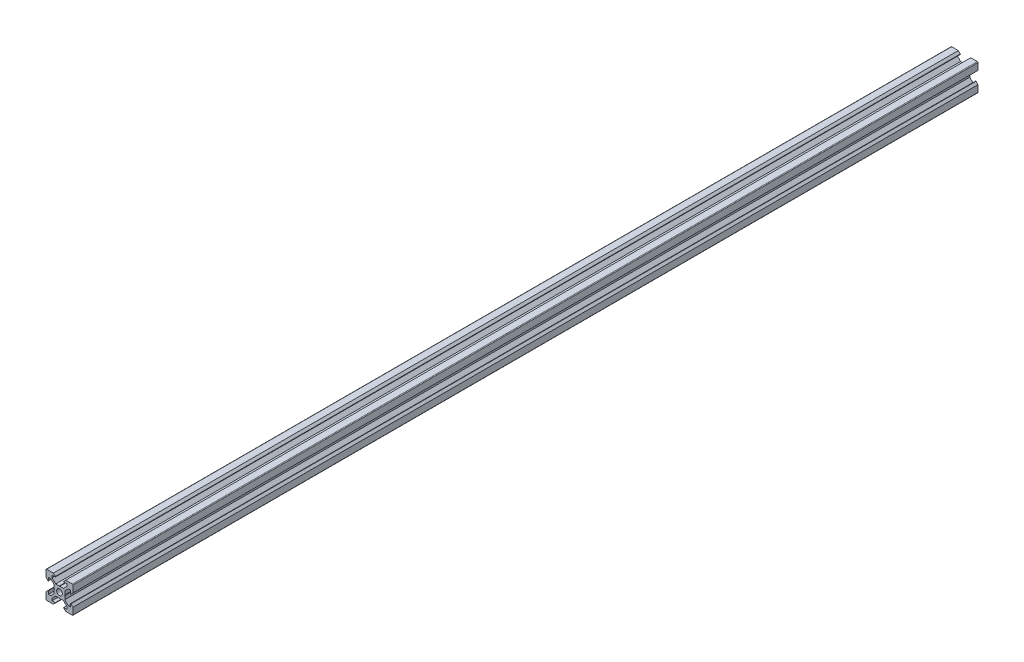
SolidWorks part; units mm, degrees
material "6061-T6 (SS)"
ref_plane "Front Plane" through (0, 0, 0) normal (0, 0, 1) x (1, 0, 0)
ref_plane "Top Plane" through (0, 0, 0) normal (0, 1, 0) x (1, 0, 0)
ref_plane "Right Plane" through (0, 0, 0) normal (1, 0, 0) x (0, 0, -1)
sketch "Sketch1" plane through (0, 0, 0) normal (0, 0, 1) x (1, 0, 0)
  line L1 (9.5, -10) -> (-9.5, -10)
  line L2 (10, -9.5) -> (10, 9.5)
  line L3 (9.5, 10) -> (-9.5, 10)
  line L4 (-10, -9.5) -> (-10, 9.5)
  line L5 (10, -10) -> (-10, 10) construction
  line L6 (10, 10) -> (-10, -10) construction
  circle A0 centre (0, 0) radius 2.1
  arc A1 (-9.5, 10) -> (-10, 9.5) centre (-9.5, 9.5) ccw
  arc A2 (10, 9.5) -> (9.5, 10) centre (9.5, 9.5) ccw
  arc A3 (9.5, -10) -> (10, -9.5) centre (9.5, -9.5) ccw
  arc A4 (-9.5, -10) -> (-10, -9.5) centre (-9.5, -9.5) cw
  point P0 (0, 0)
  line B0 (0, 0) -> (0, 10) construction
  line B1 (0, 3.69) -> (-0.21, 3.9)
  line B2 (-0.21, 3.9) -> (-2.8393, 3.9)
  line B3 (-2.8393, 3.9) -> (-5.5, 6.5607)
  line B4 (-5.5, 6.5607) -> (-5.5, 8.2)
  line B5 (-5.5, 8.2) -> (-3.125, 8.2)
  line B6 (-3.125, 8.2) -> (-3.125, 8.545)
  line B7 (-3.125, 8.545) -> (-4.58, 10)
  line B8 (-4.58, 10) -> (4.58, 10)
  line B9 (0, 0) -> (-5.9132, 5.9132) construction
  line B10 (3.125, 8.545) -> (4.58, 10)
  line B11 (3.125, 8.2) -> (3.125, 8.545)
  line B12 (5.5, 8.2) -> (3.125, 8.2)
  line B13 (5.5, 6.5607) -> (5.5, 8.2)
  line B14 (2.8393, 3.9) -> (5.5, 6.5607)
  line B15 (0.21, 3.9) -> (2.8393, 3.9)
  line B16 (0, 3.69) -> (0.21, 3.9)
  line B17 (0, 0) -> (-10, 0) construction
  line B18 (-3.69, 0) -> (-3.9, -0.21)
  line B19 (-3.9, -0.21) -> (-3.9, -2.8393)
  line B20 (-3.9, -2.8393) -> (-6.5607, -5.5)
  line B21 (-6.5607, -5.5) -> (-8.2, -5.5)
  line B22 (-8.2, -5.5) -> (-8.2, -3.125)
  line B23 (-8.2, -3.125) -> (-8.545, -3.125)
  line B24 (-8.545, -3.125) -> (-10, -4.58)
  line B25 (-10, -4.58) -> (-10, 4.58)
  line B26 (0, 0) -> (-5.9132, -5.9132) construction
  line B27 (-8.545, 3.125) -> (-10, 4.58)
  line B28 (-8.2, 3.125) -> (-8.545, 3.125)
  line B29 (-8.2, 5.5) -> (-8.2, 3.125)
  line B30 (-6.5607, 5.5) -> (-8.2, 5.5)
  line B31 (-3.9, 2.8393) -> (-6.5607, 5.5)
  line B32 (-3.9, 0.21) -> (-3.9, 2.8393)
  line B33 (-3.69, 0) -> (-3.9, 0.21)
  line B34 (0, 0) -> (0, -10) construction
  line B35 (0, -3.69) -> (0.21, -3.9)
  line B36 (0.21, -3.9) -> (2.8393, -3.9)
  line B37 (2.8393, -3.9) -> (5.5, -6.5607)
  line B38 (5.5, -6.5607) -> (5.5, -8.2)
  line B39 (5.5, -8.2) -> (3.125, -8.2)
  line B40 (3.125, -8.2) -> (3.125, -8.545)
  line B41 (3.125, -8.545) -> (4.58, -10)
  line B42 (4.58, -10) -> (-4.58, -10)
  line B43 (0, 0) -> (5.9132, -5.9132) construction
  line B44 (-3.125, -8.545) -> (-4.58, -10)
  line B45 (-3.125, -8.2) -> (-3.125, -8.545)
  line B46 (-5.5, -8.2) -> (-3.125, -8.2)
  line B47 (-5.5, -6.5607) -> (-5.5, -8.2)
  line B48 (-2.8393, -3.9) -> (-5.5, -6.5607)
  line B49 (-0.21, -3.9) -> (-2.8393, -3.9)
  line B50 (0, -3.69) -> (-0.21, -3.9)
  line B51 (0, 0) -> (10, 0) construction
  line B52 (3.69, 0) -> (3.9, 0.21)
  line B53 (3.9, 0.21) -> (3.9, 2.8393)
  line B54 (3.9, 2.8393) -> (6.5607, 5.5)
  line B55 (6.5607, 5.5) -> (8.2, 5.5)
  line B56 (8.2, 5.5) -> (8.2, 3.125)
  line B57 (8.2, 3.125) -> (8.545, 3.125)
  line B58 (8.545, 3.125) -> (10, 4.58)
  line B59 (10, 4.58) -> (10, -4.58)
  line B60 (0, 0) -> (5.9132, 5.9132) construction
  line B61 (8.545, -3.125) -> (10, -4.58)
  line B62 (8.2, -3.125) -> (8.545, -3.125)
  line B63 (8.2, -5.5) -> (8.2, -3.125)
  line B64 (6.5607, -5.5) -> (8.2, -5.5)
  line B65 (3.9, -2.8393) -> (6.5607, -5.5)
  line B66 (3.9, -0.21) -> (3.9, -2.8393)
  line B67 (3.69, 0) -> (3.9, -0.21)
  dimension "D1" = 4.2
  dimension "D3" = 0.5
  dimension "D2" = 20
sketch_block_instance "V Slot 1-4"
sketch_block "V Slot 1" parameters "D1"=10, "D2"=11, "D3"=4.3, "D4"=1.8, "D5"=0.21, "D6"=45, "D7"=9.16, "D8"=1.5, "D9"=6.25
sketch_block_instance "V Slot 1-5"
sketch_block_instance "V Slot 1-6"
sketch_block_instance "V Slot 1-7"
extrude "Boss-Extrude1" add sketch "Sketch1" along normal blind 670 contours B67 B52 B53 B54 B55 B56 B57 B58 L2 A2 L3 B10 B11 B12 B13 B14 B15 B16 B1 B2 B3 B4 B5 B6 B7 A1 L4 B27 B28 B29 B30 B31 B32 B33 B18 B19 B20 B21 B22 B23 B24 A4 L1 B44 B45 B46 B47 B48 B49
